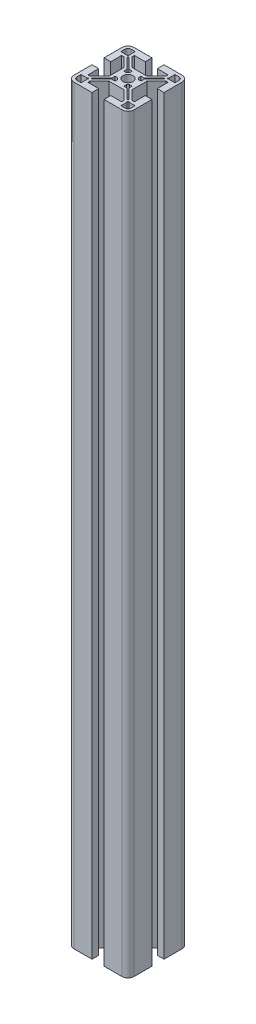
SolidWorks part; units mm, degrees
ref_plane "Ebene vorne" through (0, 0, 0) normal (0, 0, 1) x (1, 0, 0)
ref_plane "Ebene oben" through (0, 0, 0) normal (0, 1, 0) x (1, 0, 0)
ref_plane "Ebene rechts" through (0, 0, 0) normal (1, 0, 0) x (0, 0, -1)
sketch "Sketch1" plane through (0, 0, 0) normal (0, 1, 0) x (1, 0, 0)
  line L0 (-7.9326, -10.8599) -> (-58.869, -10.8599) construction
  line L1 (-7.9326, -10.8599) -> (-7.9326, 43.7859) construction
  line L2 (-7.9326, -10.8599) -> (-62.5783, 43.7859) construction
  line L3 (-27.9326, -6.8599) -> (-27.9326, 5.1401)
  line L4 (-27.9326, -6.8599) -> (-23.4326, -6.8599)
  line L5 (-23.4326, -6.8599) -> (-23.4326, 0.3901)
  line L6 (-23.4326, 0.3901) -> (-21.9326, 0.3901)
  line L7 (-21.9326, 0.3901) -> (-15.6826, -5.8599)
  line L8 (-15.6826, -5.8599) -> (-15.6826, -10.8599)
  line L9 (-25.9326, 2.3901) -> (-25.9326, 5.1401)
  line L10 (-25.9326, 2.3901) -> (-21.8897, 2.3901)
  line L11 (-21.4415, 1.9419) -> (-20.7344, 2.649)
  line L12 (-21.4415, 1.9419) -> (-21.8897, 2.3901)
  line L13 (-20.3808, 0.8813) -> (-13.6826, -5.817)
  line L14 (-13.6826, -5.817) -> (-13.6826, -7.9551)
  line L15 (-20.3808, 0.8813) -> (-19.6737, 1.5884)
  line L16 (-13.6826, -7.9551) -> (-13.1826, -7.9551)
  line L17 (-19.6737, 1.5884) -> (-12.9755, -5.1099)
  line L18 (-10.8374, -5.1099) -> (-10.8374, -5.6099)
  line L19 (-12.9755, -5.1099) -> (-10.8374, -5.1099)
  line L20 (-21.1826, 7.1401) -> (-21.1826, 3.0973)
  line L21 (-21.1826, 7.1401) -> (-23.9326, 7.1401)
  line L22 (-19.1826, 3.1401) -> (-12.9326, -3.1099)
  line L23 (-11.9326, 9.1401) -> (-11.9326, 4.6401)
  line L24 (-19.1826, 4.6401) -> (-19.1826, 3.1401)
  line L25 (-12.9326, -3.1099) -> (-7.9326, -3.1099)
  line L26 (-11.9326, 4.6401) -> (-19.1826, 4.6401)
  line L27 (-11.9326, 9.1401) -> (-23.9326, 9.1401)
  line L28 (7.5674, -6.8599) -> (7.5674, 0.3901)
  line L29 (12.0674, -6.8599) -> (12.0674, 5.1401)
  line L30 (12.0674, -6.8599) -> (7.5674, -6.8599)
  line L31 (10.0674, 2.3901) -> (10.0674, 5.1401)
  line L32 (10.0674, 2.3901) -> (6.0245, 2.3901)
  line L33 (6.0674, 0.3901) -> (-0.1826, -5.8599)
  line L34 (7.5674, 0.3901) -> (6.0674, 0.3901)
  line L35 (-0.1826, -5.8599) -> (-0.1826, -10.8599)
  line L36 (-2.1826, -5.817) -> (-2.1826, -7.9551)
  line L37 (3.8085, 1.5884) -> (-2.8897, -5.1099)
  line L38 (4.5156, 0.8813) -> (-2.1826, -5.817)
  line L39 (-2.8897, -5.1099) -> (-5.0279, -5.1099)
  line L40 (-5.0279, -5.1099) -> (-5.0279, -5.6099)
  line L41 (-2.1826, -7.9551) -> (-2.6826, -7.9551)
  line L42 (-2.9326, -3.1099) -> (-7.9326, -3.1099)
  line L43 (3.3174, 3.1401) -> (-2.9326, -3.1099)
  line L44 (5.3174, 7.1401) -> (5.3174, 3.0973)
  line L45 (5.3174, 7.1401) -> (8.0674, 7.1401)
  line L46 (-3.9326, 4.6401) -> (3.3174, 4.6401)
  line L47 (3.3174, 4.6401) -> (3.3174, 3.1401)
  line L48 (-3.9326, 9.1401) -> (8.0674, 9.1401)
  line L49 (-3.9326, 9.1401) -> (-3.9326, 4.6401)
  line L50 (-3.9326, -26.3599) -> (3.3174, -26.3599)
  line L51 (-3.9326, -30.8599) -> (8.0674, -30.8599)
  line L52 (-3.9326, -30.8599) -> (-3.9326, -26.3599)
  line L53 (5.3174, -28.8599) -> (8.0674, -28.8599)
  line L54 (5.3174, -28.8599) -> (5.3174, -24.817)
  line L55 (3.3174, -24.8599) -> (-2.9326, -18.6099)
  line L56 (3.3174, -26.3599) -> (3.3174, -24.8599)
  line L57 (-2.9326, -18.6099) -> (-7.9326, -18.6099)
  line L58 (-2.8897, -16.6099) -> (-5.0279, -16.6099)
  line L59 (4.5156, -22.601) -> (-2.1826, -15.9027)
  line L60 (3.8085, -23.3081) -> (-2.8897, -16.6099)
  line L61 (-2.1826, -15.9027) -> (-2.1826, -13.7646)
  line L62 (-2.1826, -13.7646) -> (-2.6826, -13.7646)
  line L63 (-5.0279, -16.6099) -> (-5.0279, -16.1099)
  line L64 (-0.1826, -15.8599) -> (-0.1826, -10.8599)
  line L65 (6.0674, -22.1099) -> (-0.1826, -15.8599)
  line L66 (10.0674, -24.1099) -> (6.0245, -24.1099)
  line L67 (10.0674, -24.1099) -> (10.0674, -26.8599)
  line L68 (7.5674, -14.8599) -> (7.5674, -22.1099)
  line L69 (7.5674, -22.1099) -> (6.0674, -22.1099)
  line L70 (12.0674, -14.8599) -> (12.0674, -26.8599)
  line L71 (12.0674, -14.8599) -> (7.5674, -14.8599)
  line L72 (-23.4326, -14.8599) -> (-23.4326, -22.1099)
  line L73 (-27.9326, -14.8599) -> (-27.9326, -26.8599)
  line L74 (-27.9326, -14.8599) -> (-23.4326, -14.8599)
  line L75 (-25.9326, -24.1099) -> (-25.9326, -26.8599)
  line L76 (-25.9326, -24.1099) -> (-21.8897, -24.1099)
  line L77 (-21.9326, -22.1099) -> (-15.6826, -15.8599)
  line L78 (-23.4326, -22.1099) -> (-21.9326, -22.1099)
  line L79 (-15.6826, -15.8599) -> (-15.6826, -10.8599)
  line L80 (-13.6826, -15.9027) -> (-13.6826, -13.7646)
  line L81 (-19.6737, -23.3081) -> (-12.9755, -16.6099)
  line L82 (-20.3808, -22.601) -> (-13.6826, -15.9027)
  line L83 (-12.9755, -16.6099) -> (-10.8374, -16.6099)
  line L84 (-10.8374, -16.6099) -> (-10.8374, -16.1099)
  line L85 (-13.6826, -13.7646) -> (-13.1826, -13.7646)
  line L86 (-12.9326, -18.6099) -> (-7.9326, -18.6099)
  line L87 (-19.1826, -24.8599) -> (-12.9326, -18.6099)
  line L88 (-21.1826, -28.8599) -> (-21.1826, -24.817)
  line L89 (-21.1826, -28.8599) -> (-23.9326, -28.8599)
  line L90 (-11.9326, -26.3599) -> (-19.1826, -26.3599)
  line L91 (-19.1826, -26.3599) -> (-19.1826, -24.8599)
  line L92 (-11.9326, -30.8599) -> (-23.9326, -30.8599)
  line L93 (-11.9326, -30.8599) -> (-11.9326, -26.3599)
  line L94 (-20.7344, 2.649) -> (-21.1826, 3.0973)
  line L95 (4.8692, 2.649) -> (5.3174, 3.0973)
  line L96 (4.8692, 2.649) -> (5.5763, 1.9419)
  line L97 (5.5763, 1.9419) -> (6.0245, 2.3901)
  line L98 (3.8085, 1.5884) -> (4.5156, 0.8813)
  line L99 (5.5763, -23.6616) -> (6.0245, -24.1099)
  line L100 (5.5763, -23.6616) -> (4.8692, -24.3687)
  line L101 (4.8692, -24.3687) -> (5.3174, -24.817)
  line L102 (4.5156, -22.601) -> (3.8085, -23.3081)
  line L103 (-20.7344, -24.3687) -> (-21.1826, -24.817)
  line L104 (-20.7344, -24.3687) -> (-21.4415, -23.6616)
  line L105 (-21.4415, -23.6616) -> (-21.8897, -24.1099)
  line L106 (-19.6737, -23.3081) -> (-20.3808, -22.601)
  line L107 (-13.1826, -7.9551) -> (-12.0023, -7.9551)
  line L108 (-10.8374, -5.6099) -> (-10.8374, -6.7901)
  line L109 (-5.0279, -5.6099) -> (-5.0279, -6.7901)
  line L110 (-2.6826, -7.9551) -> (-3.8629, -7.9551)
  line L111 (-2.6826, -13.7646) -> (-3.8629, -13.7646)
  line L112 (-5.0279, -16.1099) -> (-5.0279, -14.9296)
  line L113 (-10.8374, -16.1099) -> (-10.8374, -14.9296)
  line L114 (-13.1826, -13.7646) -> (-12.0023, -13.7646)
  arc A0 (-27.9326, 5.1401) -> (-23.9326, 9.1401) centre (-23.9326, 5.1401) cw
  arc A1 (-25.9326, 5.1401) -> (-23.9326, 7.1401) centre (-23.9326, 5.1401) cw
  arc A2 (-11.3326, -10.8599) -> (-7.9326, -7.4599) centre (-7.9326, -10.8599) cw
  arc A3 (-12.0023, -13.7646) -> (-10.8374, -14.9296) centre (-7.9326, -10.8599) ccw
  arc A4 (8.0674, 9.1401) -> (12.0674, 5.1401) centre (8.0674, 5.1401) cw
  arc A5 (8.0674, 7.1401) -> (10.0674, 5.1401) centre (8.0674, 5.1401) cw
  arc A6 (-5.0279, -14.9296) -> (-3.8629, -13.7646) centre (-7.9326, -10.8599) ccw
  arc A7 (-7.9326, -7.4599) -> (-4.5326, -10.8599) centre (-7.9326, -10.8599) cw
  arc A8 (12.0674, -26.8599) -> (8.0674, -30.8599) centre (8.0674, -26.8599) cw
  arc A9 (10.0674, -26.8599) -> (8.0674, -28.8599) centre (8.0674, -26.8599) cw
  arc A10 (-3.8629, -7.9551) -> (-5.0279, -6.7901) centre (-7.9326, -10.8599) ccw
  arc A11 (-4.5326, -10.8599) -> (-7.9326, -14.2599) centre (-7.9326, -10.8599) cw
  arc A12 (-23.9326, -30.8599) -> (-27.9326, -26.8599) centre (-23.9326, -26.8599) cw
  arc A13 (-23.9326, -28.8599) -> (-25.9326, -26.8599) centre (-23.9326, -26.8599) cw
  arc A14 (-10.8374, -6.7901) -> (-12.0023, -7.9551) centre (-7.9326, -10.8599) ccw
  arc A15 (-7.9326, -14.2599) -> (-11.3326, -10.8599) centre (-7.9326, -10.8599) cw
  point P19 (-20.0273, 1.2348)
  point P41 (-21.0879, 2.2955)
  point P140 (-7.9326, -10.8599)
  point P149 (-7.9326, -10.8599)
  point P152 (-7.9326, -10.8599)
extrude "Boss-Extrude1" add sketch "Sketch1" along normal blind 500 contours A12 L92 L93 L90 L91 L87 L86 L57 L55 L56 L50 L52 L51 A8 L70 L71 L68 L69 L65 L64 L35 L33 L34 L28 L30 L29 A4 L48 L49 L46 L47 L43 L42 L25 L22 L24 L26 L23 L27 A0 L3 L4 L5 L6 L7 L8 L79 L77 L78 L72 L74
